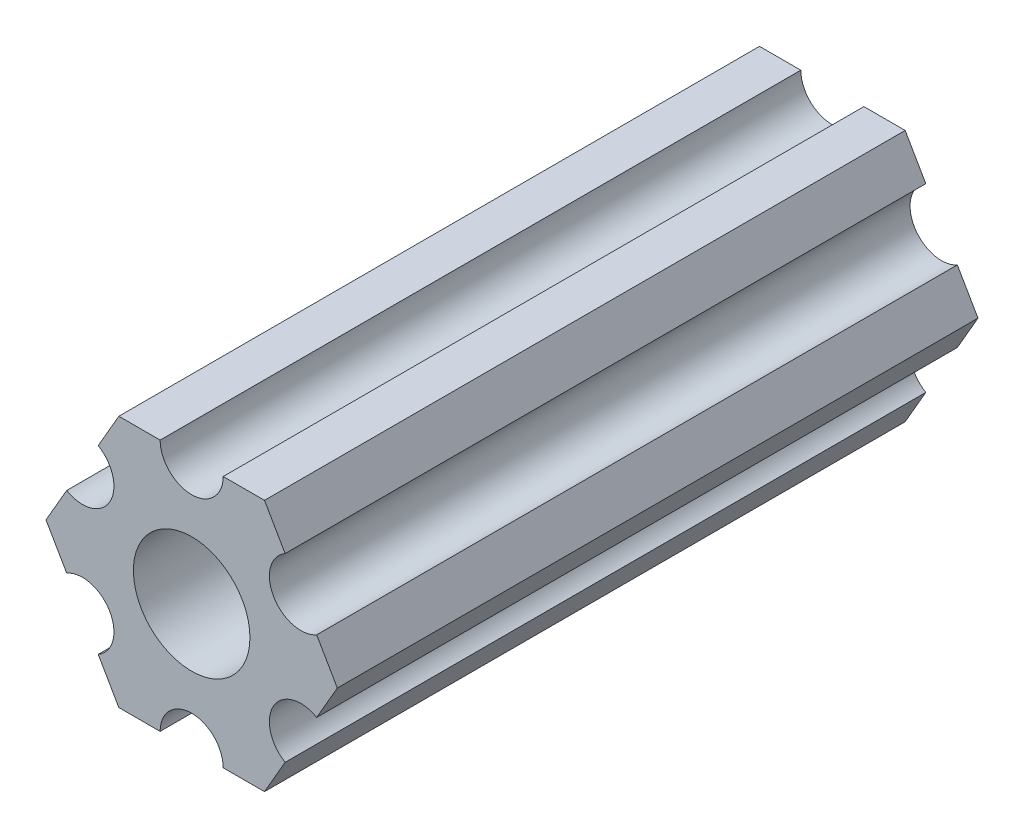
SolidWorks part; units mm, degrees
material "6061-T6 (SS)"
ref_plane "Front Plane" through (0, 0, 0) normal (0, 0, 1) x (1, 0, 0)
ref_plane "Top Plane" through (0, 0, 0) normal (0, 1, 0) x (1, 0, 0)
ref_plane "Right Plane" through (0, 0, 0) normal (1, 0, 0) x (0, 0, -1)
ref_plane "Plane1" through (0, 0, 0) normal (0, 0, -1) x (-1, 0, 0)
sketch "Sketch1" plane through (0, 0, 0) normal (0, 0, -1) x (-1, 0, 0)
  line L0 (-4.7055, -4.5498) -> (-3.6662, -6.35)
  line L1 (-3.6662, -6.35) -> (-1.5875, -6.35)
  line L2 (1.5875, -6.35) -> (3.6662, -6.35)
  line L3 (3.6662, -6.35) -> (4.7055, -4.5498)
  line L4 (6.293, -1.8002) -> (7.3323, 0)
  line L5 (7.3323, 0) -> (6.293, 1.8002)
  line L6 (4.7055, 4.5498) -> (3.6662, 6.35)
  line L7 (3.6662, 6.35) -> (1.5875, 6.35)
  line L8 (-1.5875, 6.35) -> (-3.6662, 6.35)
  line L9 (-3.6662, 6.35) -> (-4.7055, 4.5498)
  line L10 (-6.293, 1.8002) -> (-7.3323, 0)
  line L11 (-7.3323, 0) -> (-6.293, -1.8002)
  circle A0 centre (0, 0) radius 2.9337
  arc A1 (-6.293, -1.8002) -> (-4.7055, -4.5498) centre (-5.4993, -3.175) cw
  arc A2 (-1.5875, -6.35) -> (1.5875, -6.35) centre (0, -6.35) cw
  arc A3 (4.7055, -4.5498) -> (6.293, -1.8002) centre (5.4993, -3.175) cw
  arc A4 (6.293, 1.8002) -> (4.7055, 4.5498) centre (5.4993, 3.175) cw
  arc A5 (1.5875, 6.35) -> (-1.5875, 6.35) centre (0, 6.35) cw
  arc A6 (-4.7055, 4.5498) -> (-6.293, 1.8002) centre (-5.4993, 3.175) cw
extrude "Boss-Extrude1" add sketch "Sketch1" against normal blind 32.25
